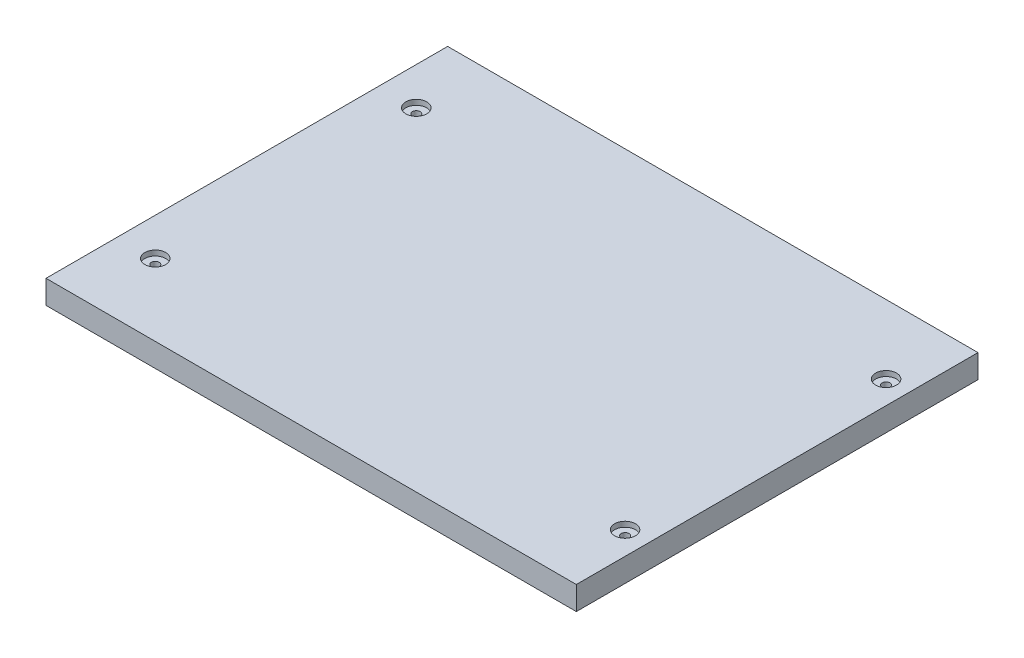
SolidWorks part; units mm, degrees
ref_plane "Front Plane" through (0, 0, 0) normal (0, 0, 1) x (1, 0, 0)
ref_plane "Top Plane" through (0, 0, 0) normal (0, 1, 0) x (1, 0, 0)
ref_plane "Right Plane" through (0, 0, 0) normal (1, 0, 0) x (0, 0, -1)
sketch "Sketch1" plane through (0, 0, 0) normal (0, 1, 0) x (1, 0, 0)
  line L1 (0, 0) -> (406.4, 0)
  line L2 (0, 0) -> (0, 307.8)
  line L3 (0, 307.8) -> (406.4, 307.8)
  line L4 (406.4, 0) -> (406.4, 307.8)
  line L5 (0, 0) -> (406.4, 307.8) construction
  line L6 (0, 307.8) -> (406.4, 0) construction
  point P4 (203.2, 153.9)
  dimension "D1" = 307.8
  dimension "D2" = 406.4
extrude "Boss-Extrude1" add sketch "Sketch1" along normal blind 18
sketch "Sketch2" plane through (0, 18, 0) normal (0, 1, 0) x (1, 0, 0)
  line L0 (0, 0) -> (28.75, 0) construction
  line L1 (0, 0) -> (406.4, 0) construction
  line L2 (28.75, 0) -> (28.75, 55) construction
  line L3 (28.75, 55) -> (28.75, 255) construction
  line L4 (28.75, 255) -> (388.75, 255) construction
  line L5 (388.75, 255) -> (388.75, 55) construction
  line L6 (388.75, 55) -> (28.75, 55) construction
  circle A0 centre (28.75, 55) radius 8
  circle A1 centre (388.75, 255) radius 8
  circle A2 centre (388.75, 55) radius 8
  circle A3 centre (28.75, 255) radius 8
  dimension "D3" = 16
  dimension "D1" = 28.75
  dimension "D2" = 55
  dimension "D4" = 200
  dimension "D5" = 360
extrude "Cut-Extrude1" cut sketch "Sketch2" against normal blind 4
sketch "Sketch3" plane through (0, 14, 0) normal (0, 1, 0) x (1, 0, 0)
  circle A0 centre (388.75, 55) radius 8 construction
  circle A1 centre (28.75, 255) radius 8
  circle A2 centre (28.75, 255) radius 8
  circle A3 centre (28.75, 55) radius 8
  circle A4 centre (28.75, 55) radius 8
  circle A5 centre (388.75, 255) radius 8 construction
  circle A6 centre (388.75, 55) radius 8
  circle A7 centre (388.75, 255) radius 8
  circle A8 centre (28.75, 255) radius 3
  circle A9 centre (388.75, 255) radius 3
  circle A10 centre (388.75, 55) radius 3
  circle A11 centre (28.75, 55) radius 3
  dimension "D3" = 6
  dimension "D1" = 0
  dimension "D2" = 0
extrude "Cut-Extrude2" cut sketch "Sketch3" against normal through all both and the other way through all contours A8 | A11 | A10 | A9
